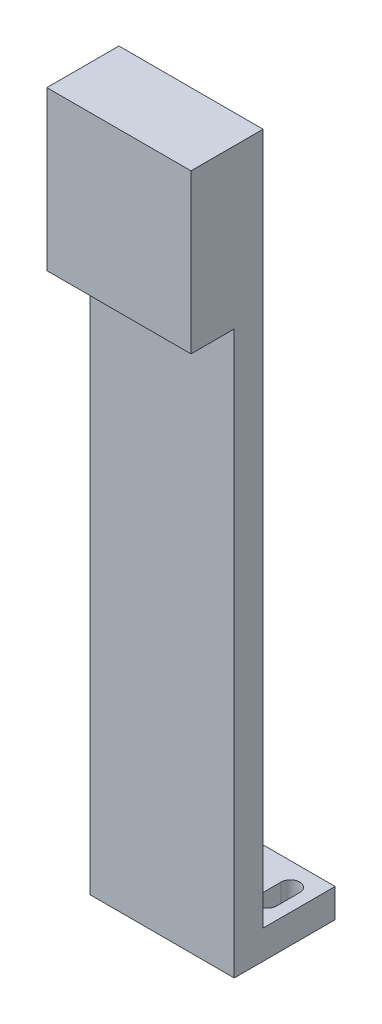
SolidWorks part; units mm, degrees
ref_plane "前视基准面" through (0, 0, 0) normal (0, 0, 1) x (1, 0, 0)
ref_plane "上视基准面" through (0, 0, 0) normal (0, 1, 0) x (1, 0, 0)
ref_plane "右视基准面" through (0, 0, 0) normal (1, 0, 0) x (0, 0, -1)
sketch "草图1" plane through (0, 0, 0) normal (0, 1, 0) x (1, 0, 0)
  line L1 (25, -17.5) -> (-25, -17.5)
  line L2 (25, -17.5) -> (25, 17.5)
  line L3 (25, 17.5) -> (-25, 17.5)
  line L4 (-25, -17.5) -> (-25, 17.5)
  line L5 (25, -17.5) -> (-25, 17.5) construction
  line L6 (25, 17.5) -> (-25, -17.5) construction
  point P0 (0, 0)
  dimension "D1" = 50
  dimension "D2" = 35
extrude "凸台-拉伸1" add sketch "草图1" along normal blind 250
sketch "草图2" plane through (0, 250, 0) normal (0, 1, 0) x (1, 0, 0)
  line L0 (25, -17.5) -> (25, 17.5) construction
  line L1 (-25, 17.5) -> (25, 17.5)
  line L2 (-25, 17.5) -> (-25, -7.5)
  line L3 (-25, -7.5) -> (25, -7.5)
  line L4 (25, 17.5) -> (25, -7.5)
  line L5 (-25, -17.5) -> (25, -17.5) construction
  dimension "D1" = 10
extrude "切除-拉伸1" cut sketch "草图2" against normal offset from surface (240 mm away) 10 up to face at (0, 0, 0)
sketch "草图3" plane through (0, 10, 0) normal (0, 1, 0) x (1, 0, 0)
  line L0 (0, 17.5) -> (0, 5.5) construction
  line L1 (-25, 17.5) -> (25, 17.5) construction
  line L2 (0, 5.5) -> (-17.5, 5.5) construction
  line L3 (-17.5, 1.5) -> (-17.5, 9.5) construction
  line L4 (-20.7, 1.5) -> (-20.7, 9.5)
  line L5 (-14.3, 1.5) -> (-14.3, 9.5)
  line L6 (17.5, 1.5) -> (17.5, 9.5) construction
  line L7 (20.7, 1.5) -> (20.7, 9.5)
  line L8 (14.3, 1.5) -> (14.3, 9.5)
  arc A0 (-20.7, 1.5) -> (-14.3, 1.5) centre (-17.5, 1.5) ccw
  arc A1 (-14.3, 9.5) -> (-20.7, 9.5) centre (-17.5, 9.5) ccw
  arc A2 (20.7, 1.5) -> (14.3, 1.5) centre (17.5, 1.5) cw
  arc A3 (14.3, 9.5) -> (20.7, 9.5) centre (17.5, 9.5) cw
  point P8 (-17.5, 5.5)
  point P15 (17.5, 5.5)
  dimension "D2" = 3.2
  dimension "D1" = 35
  dimension "D3" = 8
  dimension "D4" = 12
extrude "切除-拉伸2" cut sketch "草图3" against normal through all
sketch "草图4" plane through (0, 0, 7.5) normal (0, 0, -1) x (-1, 0, 0)
  line L0 (0, 250) -> (0, 210) construction
  line L1 (25, 250) -> (-25, 250) construction
  circle A0 centre (0, 210) radius 4.5949
  circle A1 centre (0, 240) radius 3.3452
  dimension "D1" = 30
  dimension "D2" = 10
sketch "草图5" plane through (0, 0, 17.5) normal (0, 0, 1) x (1, 0, 0)
  line L0 (25, 250) -> (25, 0) construction
  line L1 (-25, 250) -> (25, 250)
  line L2 (-25, 250) -> (-25, 195)
  line L3 (-25, 195) -> (25, 195)
  line L4 (25, 250) -> (25, 195)
  dimension "D1" = 55
extrude "凸台-拉伸2" add sketch "草图5" along normal blind 15
